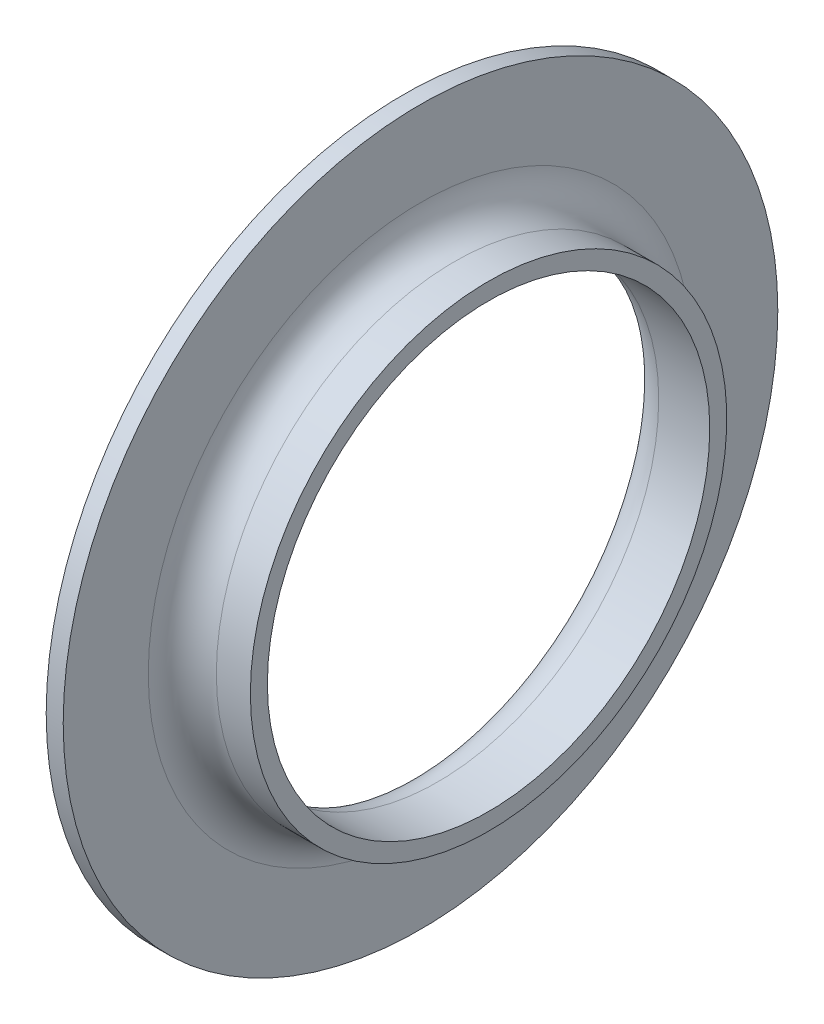
SolidWorks part; units mm, degrees
material "Сталь 10 ГОСТ 535-88"
ref_plane "Спереди" through (0, 0, 0) normal (0, 0, 1) x (1, 0, 0)
ref_plane "Сверху" through (0, 0, 0) normal (0, 1, 0) x (1, 0, 0)
ref_plane "Справа" through (0, 0, 0) normal (1, 0, 0) x (0, 0, -1)
sketch "Эскиз2" plane through (0, 0, 0) normal (0, 0, 1) x (1, 0, 0)
  line L0 (0, 0) -> (57.7851, 0) construction
  line L1 (0, 21) -> (0, 15)
  line L2 (2, 13) -> (5, 13)
  line L3 (5, 13) -> (5, 14)
  line L4 (5, 14) -> (3, 14)
  line L5 (1, 16) -> (1, 21)
  line L6 (1, 21) -> (0, 21)
  arc A0 (2, 13) -> (0, 15) centre (2, 15) cw
  arc A1 (3, 14) -> (1, 16) centre (3, 16) cw
  point P11 (0, 13)
  dimension "D6" = 2
  dimension "D1" = 1
  dimension "D2" = 13
  dimension "D3" = 1
  dimension "D4" = 21
  dimension "D5" = 5
revolve "Повернуть1" add sketch "Эскиз2" angle 360 about L0
